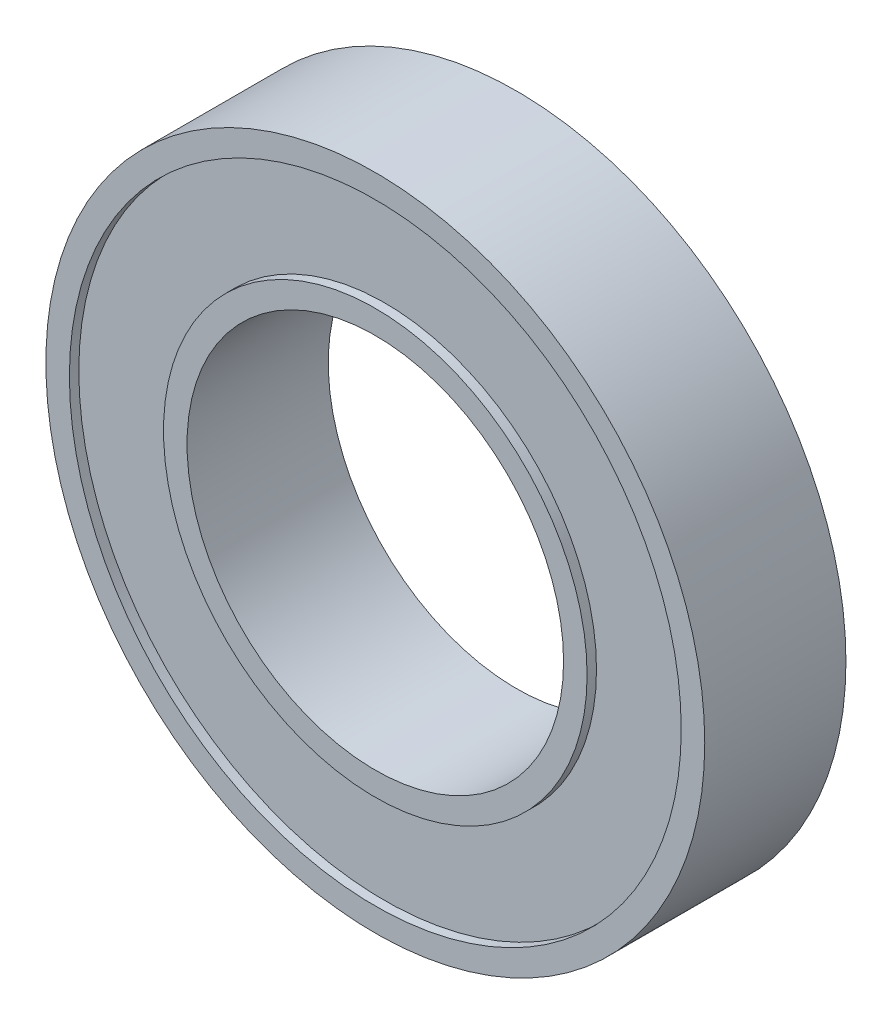
SolidWorks part; units mm, degrees
ref_plane "Front Plane" through (0, 0, 0) normal (0, 0, 1) x (1, 0, 0)
ref_plane "Top Plane" through (0, 0, 0) normal (0, 1, 0) x (1, 0, 0)
ref_plane "Right Plane" through (0, 0, 0) normal (1, 0, 0) x (0, 0, -1)
sketch "Sketch1" plane through (0, 0, 0) normal (0, 0, 1) x (1, 0, 0)
  circle A0 centre (0, 0) radius 35
  circle A1 centre (0, 0) radius 20
  dimension "D1" = 70
  dimension "D2" = 40
extrude "Boss-Extrude1" add sketch "Sketch1" along normal mid plane 15
sketch "Sketch2" plane through (0, 0, 7.5) normal (0, 0, 1) x (1, 0, 0)
  circle A0 centre (0, 0) radius 32.5
  circle A1 centre (0, 0) radius 22.5
  dimension "D1" = 45
  dimension "D2" = 65
extrude "Cut-Extrude1" cut sketch "Sketch2" against normal blind 1
mirror "Mirror1" about plane through (0, 0, 0) normal (0, 0, 1) of "Cut-Extrude1"
